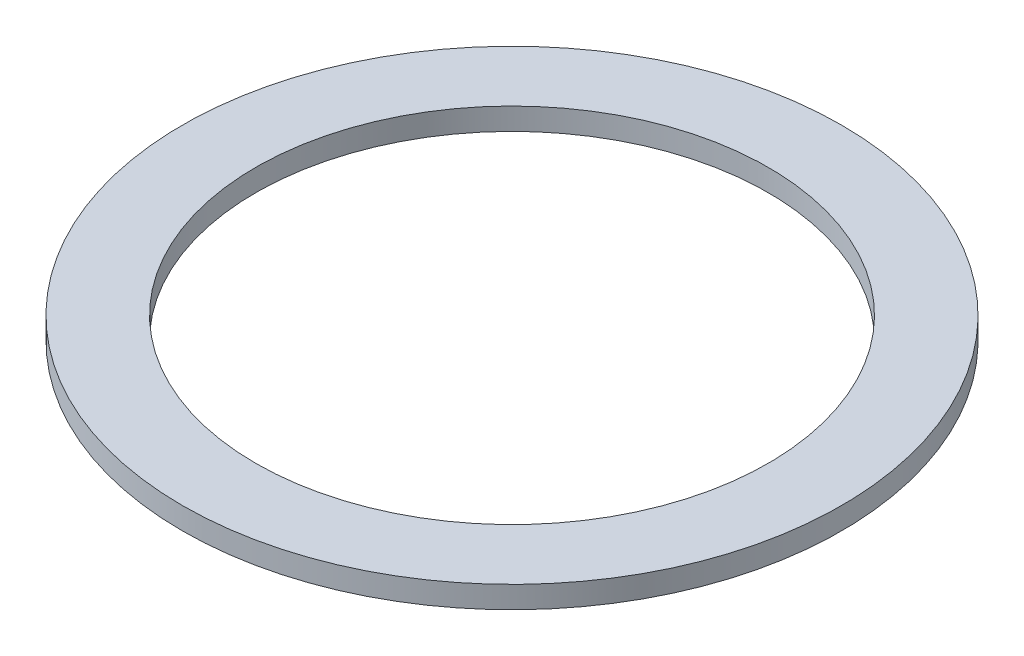
SolidWorks part; units mm, degrees
material "Acrílico (Impacto medio-alto)"
ref_plane "Alzado" through (0, 0, 0) normal (0, 0, 1) x (1, 0, 0)
ref_plane "Planta" through (0, 0, 0) normal (0, 1, 0) x (1, 0, 0)
ref_plane "Vista lateral" through (0, 0, 0) normal (1, 0, 0) x (0, 0, -1)
sketch "Croquis1" plane through (0, 0, 0) normal (0, 1, 0) x (1, 0, 0)
  circle A0 centre (0, 0) radius 45
  circle A1 centre (0, 0) radius 35
  dimension "D1" = 90
  dimension "D2" = 10
extrude "Saliente-Extruir1" add sketch "Croquis1" along normal blind 3 contours A1
equation "\"Espesor Acrilico\"= 3mm"
